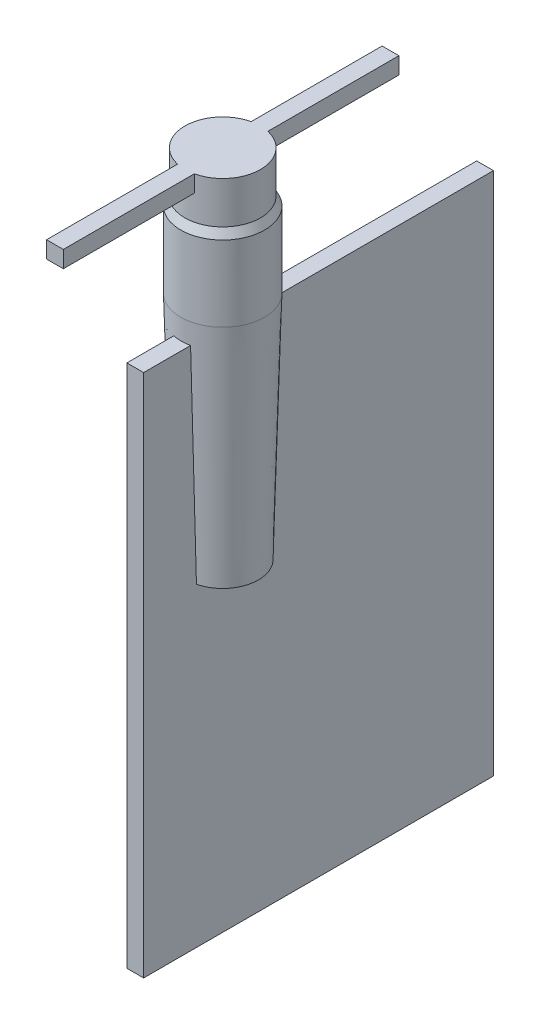
SolidWorks part; units mm, degrees
ref_plane "前视基准面" through (0, 0, 0) normal (0, 0, 1) x (1, 0, 0)
ref_plane "上视基准面" through (0, 0, 0) normal (0, 1, 0) x (1, 0, 0)
ref_plane "右视基准面" through (0, 0, 0) normal (1, 0, 0) x (0, 0, -1)
other "Configuration Table"
sketch "草图8" plane through (0, 0, 0) normal (0, 1, 0) x (1, 0, 0)
  circle A0 centre (0, 0) radius 450
  dimension "D1" = 900
extrude "凸台-拉伸3" add sketch "草图8" against normal blind 500
sketch "草图9" [suppressed] plane through (0, 0, 0) normal (0, 1, 0) x (1, 0, 0)
  line L0 (-1, -2) -> (-1, 2)
  line L1 (-1, -2) -> (1, -2)
  line L2 (-1, 2) -> (1, 2)
  line L3 (1, -2) -> (1, 2)
  line L4 (-1, -2) -> (1, 2) construction
  line L5 (-1, 2) -> (1, -2) construction
  line L6 (0, 2) -> (0, -2) construction
  point P1 (0, 0)
  dimension "D1" = 4
  dimension "D2" = 2
extrude "凸台-拉伸4" [suppressed] add sketch "草图9" against normal blind 0.2
sketch "草图19" plane through (0, 0, 0) normal (1, 0, 0) x (0, 0, -1)
  line L0 (450, -500) -> (500, -600)
  line L1 (500, -600) -> (500, -1500)
  line L2 (500, -1500) -> (0, -1500)
  line L3 (0, -1500) -> (0, -500)
  line L4 (-450, -500) -> (450, -500) construction
  line L5 (0, -500) -> (450, -500)
  dimension "D1" = 100
  dimension "D2" = 1000
  dimension "D3" = 500
revolve "旋转1" add sketch "草图19" angle 360 about L3
ref_plane "基准面4" through (0, -4250, 0) normal (0, -1, 0) x (-1, 0, 0)
sketch "草图20" plane through (0, -4250, 0) normal (0, -1, 0) x (-1, 0, 0)
  circle A0 centre (0, 0) radius 425
  dimension "D1" = 850
sketch "草图21" plane through (0, 0, 0) normal (1, 0, 0) x (0, 0, -1)
  line L0 (-425, -4250) -> (425, -4250) construction
  line L1 (-500, -1500) -> (500, -1500) construction
  line L2 (-425, -4250) -> (425, -4250)
  line L3 (-500, -1500) -> (500, -1500)
  line L4 (-425, -4250) -> (-500, -1500)
loft "放样2" add profiles "草图20" section edge at (0, -1500, -500) section "草图20"
sketch "草图22" plane through (0, 0, 0) normal (1, 0, 0) x (0, 0, -1)
  line L0 (500, -1500) -> (-500, -1500) construction
  line L1 (-1042.5, -1750) -> (3127.5, -1750)
  line L2 (-1042.5, -1750) -> (-1042.5, -8000)
  line L3 (-1042.5, -8000) -> (3127.5, -8000)
  line L4 (3127.5, -1750) -> (3127.5, -8000)
  line L5 (0, -1500) -> (0, -4250) construction
  dimension "D1" = 250
  dimension "D2" = 6250
  dimension "D3" = 4170
  dimension "D4" = 1042.5
extrude "凸台-拉伸9" add sketch "草图22" along normal mid plane 200
sketch "草图23" plane through (0, 0, 0) normal (0, 1, 0) x (1, 0, 0)
  line L1 (-650, 650) -> (650, 650)
  line L2 (-650, 650) -> (-650, -650)
  line L3 (-650, -650) -> (650, -650)
  line L4 (650, 650) -> (650, -650)
  line L5 (-650, 650) -> (650, -650) construction
  line L6 (-650, -650) -> (650, 650) construction
  circle A0 centre (0, 0) radius 520
  circle A1 centre (0, 0) radius 450 construction
  dimension "D3" = 70
  dimension "D1" = 1300
  dimension "D2" = 1300
extrude "凸台-拉伸10" [suppressed] add sketch "草图23" against normal blind 500 separate body
ref_plane "基准面5" through (0, -600, 0) normal (0, 1, 0) x (1, 0, 0)
sketch "草图24" plane through (0, -600, 0) normal (0, 1, 0) x (1, 0, 0)
  line L1 (650, -650) -> (-650, -650)
  line L2 (650, -650) -> (650, 650)
  line L3 (650, 650) -> (-650, 650)
  line L4 (-650, -650) -> (-650, 650)
  line L5 (650, -650) -> (-650, 650) construction
  line L6 (650, 650) -> (-650, -650) construction
  circle A0 centre (0, 0) radius 570
  circle A1 centre (0, 0) radius 500 construction
  dimension "D1" = 70
  dimension "D2" = 1300
  dimension "D3" = 1300
extrude "凸台-拉伸11" [suppressed] add sketch "草图24" against normal blind 1000 separate body
fillet "圆角1" [suppressed] radius 600
fillet "圆角2" [suppressed] radius 600
sketch "草图25" plane through (0, 0, 0) normal (0, 1, 0) x (1, 0, 0)
  line L1 (-100, -2000) -> (100, -2000)
  line L2 (-100, -2000) -> (-100, 2000)
  line L3 (-100, 2000) -> (100, 2000)
  line L4 (100, -2000) -> (100, 2000)
  line L5 (-100, -2000) -> (100, 2000) construction
  line L6 (-100, 2000) -> (100, -2000) construction
  point P0 (0, 0)
  dimension "D1" = 4000
  dimension "D2" = 200
extrude "凸台-拉伸12" add sketch "草图25" against normal blind 200
